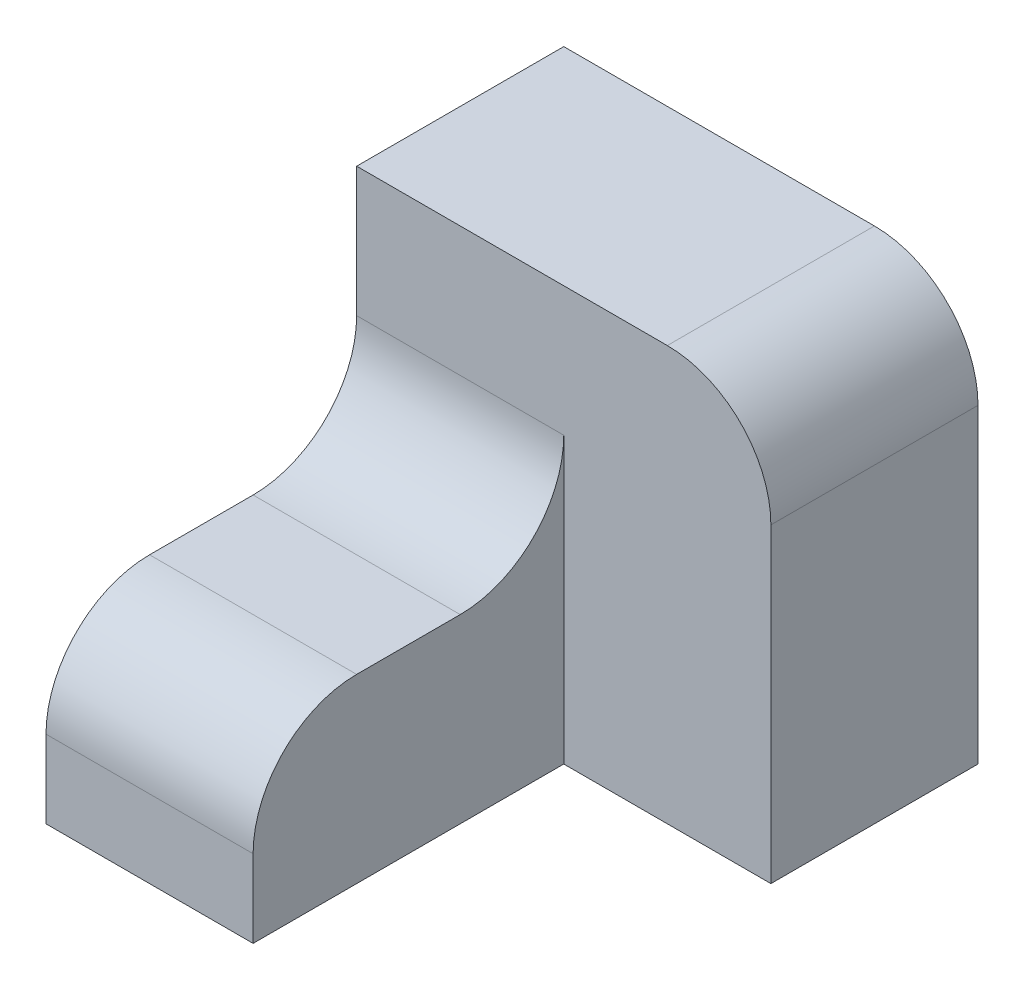
SolidWorks part; units mm, degrees
ref_plane "Front Plane" through (0, 0, 0) normal (0, 0, 1) x (1, 0, 0)
ref_plane "Top Plane" through (0, 0, 0) normal (0, 1, 0) x (1, 0, 0)
ref_plane "Right Plane" through (0, 0, 0) normal (1, 0, 0) x (0, 0, -1)
sketch "Sketch1" plane through (0, 0, 0) normal (0, 0, 1) x (1, 0, 0)
  line L1 (-30, -17.5) -> (-10, -17.5)
  line L2 (-10, -17.5) -> (-10, 0)
  line L3 (-10, 0) -> (-30, 0)
  line L4 (-30, 0) -> (-30, -17.5)
  dimension "D1" = 20
  dimension "Width" = 17.5
extrude "Boss-Extrude1" add sketch "Sketch1" along normal blind 30
sketch "Sketch2" plane through (0, 0, 0) normal (0, 0, 1) x (1, 0, 0)
  line L1 (-30, -17.5) -> (10, -17.5)
  line L2 (10, -17.5) -> (10, 22.5)
  line L3 (10, 22.5) -> (-30, 22.5)
  line L4 (-30, 22.5) -> (-30, -17.5)
  dimension "D1" = 40
  dimension "Width" = 40
extrude "Boss-Extrude2" add sketch "Sketch2" against normal blind 20
fillet "Fillet1" radius 10 3 edges at (-20, 0, 0) (10, 22.5, -10) (-20, 0, 30)
